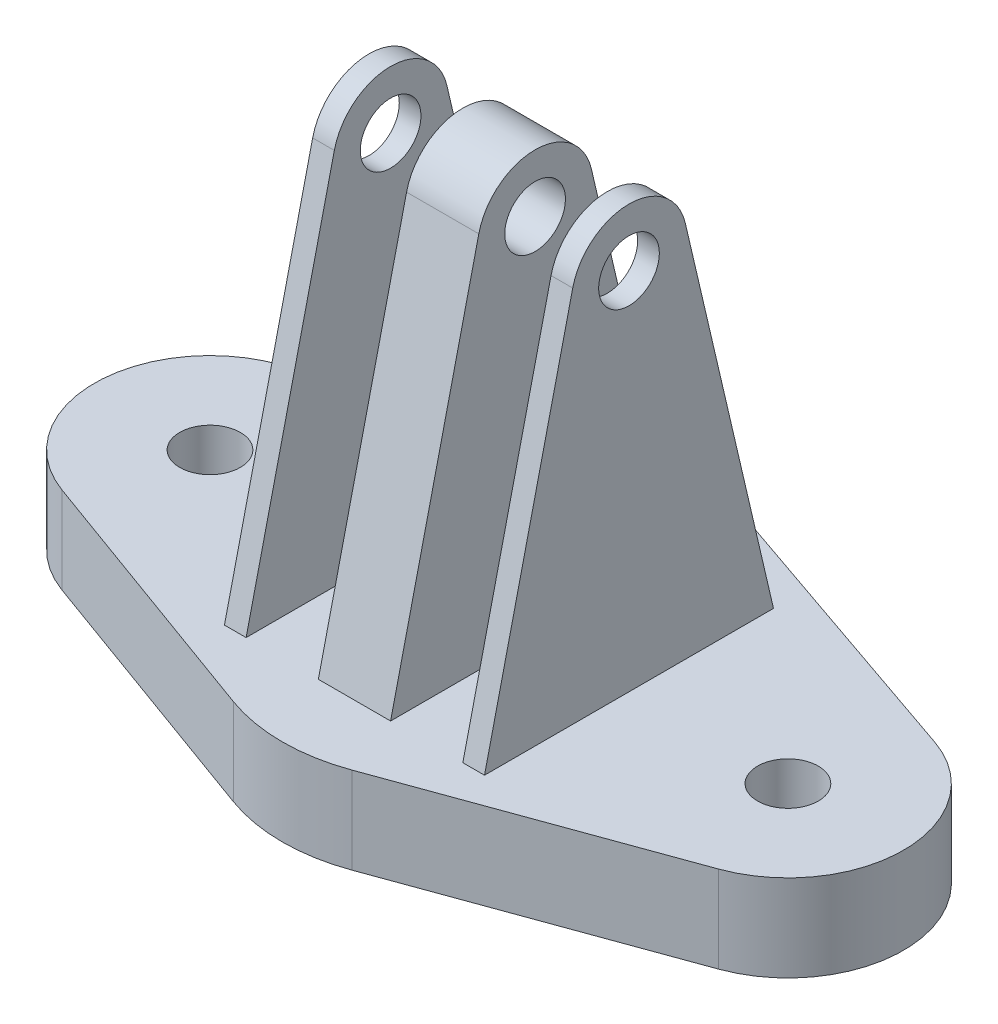
SolidWorks part; units mm, degrees
ref_plane "Front Plane" through (0, 0, 0) normal (0, 0, 1) x (1, 0, 0)
ref_plane "Top Plane" through (0, 0, 0) normal (0, 1, 0) x (1, 0, 0)
ref_plane "Right Plane" through (0, 0, 0) normal (1, 0, 0) x (0, 0, -1)
sketch "Sketch1" plane through (0, 0, 0) normal (0, 1, 0) x (1, 0, 0)
  line L0 (22.604, 7.5644) -> (1.953, 14.6733)
  line L5 (0, -39.2644) -> (0, 49.8899) construction
  line L6 (22.7281, -7.5205) -> (4.0921, -14.2807)
  line L7 (0, 15) -> (0, -15)
  arc A0 (1.953, 14.6733) -> (0, 15) centre (0, 9) ccw
  arc A1 (22.604, 7.5644) -> (22.7281, -7.5205) centre (20, 0) cw
  arc A2 (4.0921, -14.2807) -> (0, -15) centre (0, -3) cw
  circle A3 centre (20, 0) radius 2.1
  point P0 (0, 0)
  point P13 (0, 0)
  dimension "D2" = 4.2
  dimension "D3" = 8
  dimension "D4" = 6
  dimension "D5" = 12
  dimension "D1" = 20
  dimension "D6" = 30
extrude "Boss-Extrude1" add sketch "Sketch1" along normal blind 6
mirror "Mirror1" about plane through (0, 6, -15) normal (1, 0, 0) of "Boss-Extrude1"
sketch "Sketch2" plane through (0, 0, 0) normal (1, 0, 0) x (0, 0, -1)
  line L0 (-10, 6) -> (-3.8953, 32.1494)
  line L1 (7.5644, 6) -> (-7.5205, 6) construction
  line L2 (3.8953, 32.1494) -> (10, 6)
  line L3 (10, 6) -> (-10, 6)
  arc A0 (-3.8953, 32.1494) -> (3.8953, 32.1494) centre (0, 31.24) cw
  circle A1 centre (0, 31.24) radius 2.1
  point P6 (0, 6)
  dimension "D1" = 4
  dimension "D2" = 4.2
  dimension "D3" = 20
  dimension "D4" = 25.24
extrude "Boss-Extrude2" add sketch "Sketch2" along normal mid plane 18
sketch "Sketch3" plane through (0, 0, 0) normal (0, 0, 1) x (1, 0, 0)
  line L0 (9, 35.24) -> (-9, 35.24) construction
  line L1 (-7.5, 64.48) -> (-2.5, 64.48)
  line L2 (-7.5, 64.48) -> (-7.5, 6)
  line L3 (-7.5, 6) -> (-2.5, 6)
  line L4 (-2.5, 64.48) -> (-2.5, 6)
  line L5 (-7.5, 64.48) -> (-2.5, 6) construction
  line L6 (-7.5, 6) -> (-2.5, 64.48) construction
  line L7 (-4.0921, 6) -> (-22.7281, 6) construction
  point P0 (-5, 35.24)
  dimension "D1" = 5
  dimension "D2" = 2.5
extrude "Cut-Extrude1" cut sketch "Sketch3" against normal through all both and the other way through all
mirror "Mirror2" about plane through (0, 0, 0) normal (1, 0, 0) of "Cut-Extrude1"
